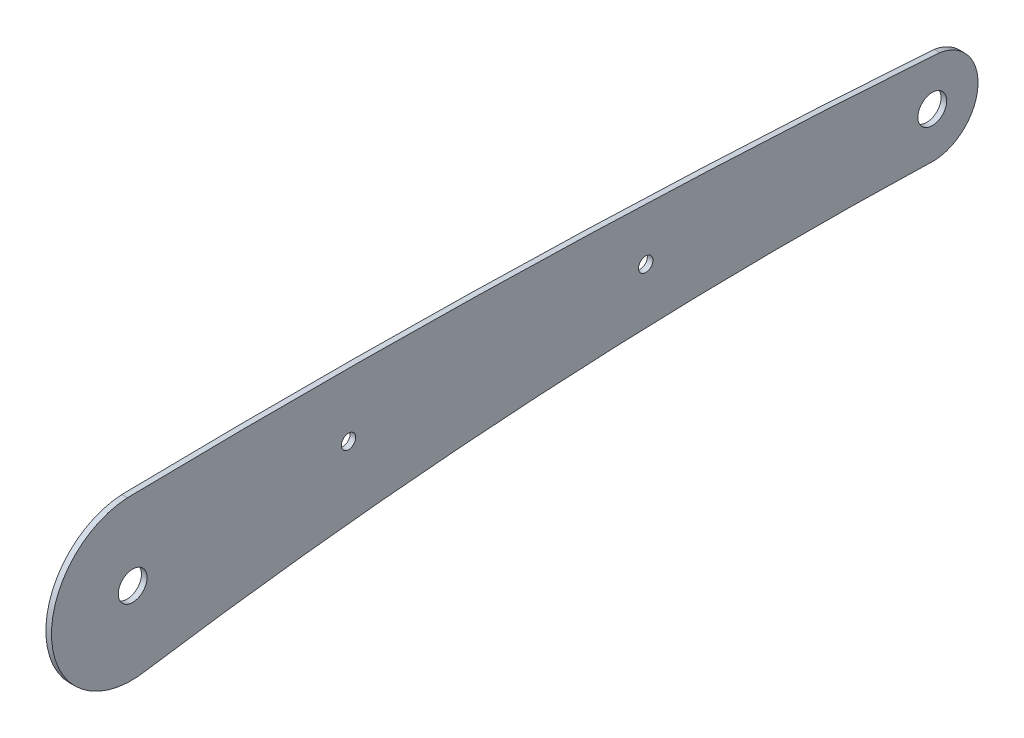
SolidWorks part; units mm, degrees
ref_plane "前基準面" through (0, 0, 0) normal (0, 0, 1) x (1, 0, 0)
ref_plane "上基準面" through (0, 0, 0) normal (0, 1, 0) x (1, 0, 0)
ref_plane "右基準面" through (0, 0, 0) normal (1, 0, 0) x (0, 0, -1)
sketch "草圖1" plane through (0, 0, 0) normal (1, 0, 0) x (0, 0, -1)
  circle A6 centre (-102.144, 0.1333) radius 3.85
  circle A8 centre (35.0011, 5.9829) radius 1.925
  circle A9 centre (-44.4328, 4.6867) radius 1.925
  arc A10 (111.556, -8.572) -> (-98.2301, -21.2449) centre (76.1692, -1165.5062) ccw
  arc A11 (-103.5418, 21.202) -> (-98.2301, -21.2449) centre (-102.3984, -0.2107) ccw
  arc A12 (111.556, -8.572) -> (112.407, -8.5887) centre (112.0794, -3.5995) ccw
  arc A13 (112.407, -8.5887) -> (113.5845, 15.6966) centre (111.6053, 3.6213) ccw
  arc A14 (113.5845, 15.6966) -> (-103.5418, 21.202) centre (-56.6324, -2413.0729) ccw
  circle A15 centre (111.6053, 3.6213) radius 3.85
extrude "填料-伸長1" add sketch "草圖1" along normal blind 1.5
